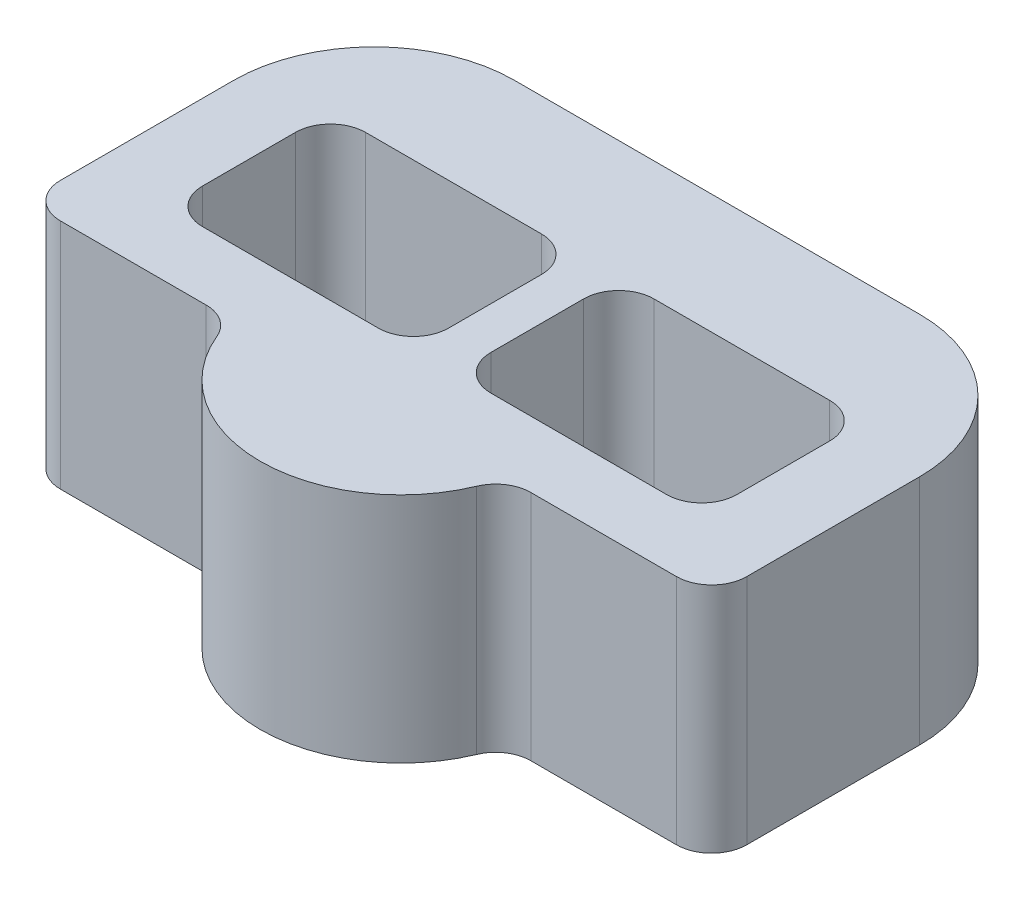
SolidWorks part; units mm, degrees
ref_plane "Front Plane" through (0, 0, 0) normal (0, 0, 1) x (1, 0, 0)
ref_plane "Top Plane" through (0, 0, 0) normal (0, 1, 0) x (1, 0, 0)
ref_plane "Right Plane" through (0, 0, 0) normal (1, 0, 0) x (0, 0, -1)
sketch "Sketch1" plane through (0, 0, 0) normal (0, 1, 0) x (1, 0, 0)
  line L1 (13.208, -13.716) -> (22.733, -13.716) construction
  line L2 (0, -8.255) -> (0, -23.876)
  line L3 (45.6459, -27.051) -> (58.801, -27.051)
  line L4 (61.976, -8.255) -> (61.976, -23.876)
  line L5 (10.033, -6.35) -> (25.908, -6.35) construction
  line L6 (6.858, -9.525) -> (6.858, -17.907) construction
  line L7 (12.7, 4.445) -> (49.276, 4.445)
  line L8 (10.033, -21.082) -> (25.908, -21.082) construction
  line L10 (29.083, -9.525) -> (29.083, -17.907) construction
  line L11 (55.118, -9.525) -> (55.118, -17.907) construction
  line L12 (51.943, -21.082) -> (36.068, -21.082) construction
  line L13 (32.893, -9.525) -> (32.893, -17.907) construction
  line L14 (51.943, -6.35) -> (36.068, -6.35) construction
  line L15 (3.175, -27.051) -> (16.3301, -27.051)
  line L16 (13.208, -10.541) -> (22.733, -10.541)
  line L17 (13.208, -16.891) -> (22.733, -16.891)
  line L18 (30.988, 4.445) -> (30.988, -36.83) construction
  line L19 (48.768, -13.716) -> (39.243, -13.716) construction
  line L20 (48.768, -10.541) -> (39.243, -10.541)
  line L21 (48.768, -16.891) -> (39.243, -16.891)
  arc A0 (19.2617, -29.0068) -> (42.7143, -29.0068) centre (30.988, -24.13) ccw
  arc A3 (0, -8.255) -> (12.7, 4.445) centre (12.7, -8.255) cw
  arc A4 (61.976, -8.255) -> (49.276, 4.445) centre (49.276, -8.255) ccw
  arc A5 (3.175, -27.051) -> (0, -23.876) centre (3.175, -23.876) cw
  arc A6 (58.801, -27.051) -> (61.976, -23.876) centre (58.801, -23.876) ccw
  arc A7 (42.7143, -29.0068) -> (45.6459, -27.051) centre (45.6459, -30.226) cw
  arc A8 (19.2617, -29.0068) -> (16.3301, -27.051) centre (16.3301, -30.226) ccw
  arc A9 (55.118, -17.907) -> (51.943, -21.082) centre (51.943, -17.907) cw construction
  arc A10 (55.118, -9.525) -> (51.943, -6.35) centre (51.943, -9.525) ccw construction
  arc A11 (36.068, -21.082) -> (32.893, -17.907) centre (36.068, -17.907) cw construction
  arc A12 (32.893, -9.525) -> (36.068, -6.35) centre (36.068, -9.525) cw construction
  arc A13 (25.908, -6.35) -> (29.083, -9.525) centre (25.908, -9.525) cw construction
  arc A14 (25.908, -21.082) -> (29.083, -17.907) centre (25.908, -17.907) ccw construction
  arc A15 (6.858, -17.907) -> (10.033, -21.082) centre (10.033, -17.907) ccw construction
  arc A16 (10.033, -6.35) -> (6.858, -9.525) centre (10.033, -9.525) ccw construction
  arc A17 (13.208, -10.541) -> (13.208, -16.891) centre (13.208, -13.716) ccw
  arc A18 (22.733, -16.891) -> (22.733, -10.541) centre (22.733, -13.716) ccw
  arc A19 (48.768, -10.541) -> (48.768, -16.891) centre (48.768, -13.716) cw
  arc A20 (39.243, -16.891) -> (39.243, -10.541) centre (39.243, -13.716) cw
  point P27 (0, 0)
  point P34 (43.3475, -27.051)
  point P55 (17.9705, -13.716)
  point P60 (6.858, -13.716)
  point P65 (44.0055, -13.716)
  dimension "D1" = 12.7
extrude "Boss-Extrude1" add sketch "Sketch1" along normal blind 20.9804
sketch "Sketch2" plane through (0, 20.9804, 0) normal (0, 1, 0) x (1, 0, 0)
  line L0 (6.858, -9.525) -> (6.858, -17.907) construction
  line L1 (10.033, -21.082) -> (25.908, -21.082) construction
  line L2 (29.083, -9.525) -> (29.083, -17.907) construction
  line L3 (10.033, -6.35) -> (25.908, -6.35) construction
  line L4 (6.858, -9.525) -> (6.858, -17.907)
  line L5 (10.033, -21.082) -> (25.908, -21.082)
  line L6 (29.083, -9.525) -> (29.083, -17.907)
  line L7 (10.033, -6.35) -> (25.908, -6.35)
  line L8 (51.943, -6.35) -> (36.068, -6.35) construction
  line L9 (32.893, -9.525) -> (32.893, -17.907) construction
  line L10 (51.943, -21.082) -> (36.068, -21.082) construction
  line L11 (55.118, -9.525) -> (55.118, -17.907) construction
  line L12 (51.943, -6.35) -> (36.068, -6.35)
  line L13 (32.893, -9.525) -> (32.893, -17.907)
  line L14 (51.943, -21.082) -> (36.068, -21.082)
  line L15 (55.118, -9.525) -> (55.118, -17.907)
  arc A0 (10.033, -6.35) -> (6.858, -9.525) centre (10.033, -9.525) ccw construction
  arc A1 (6.858, -17.907) -> (10.033, -21.082) centre (10.033, -17.907) ccw construction
  arc A2 (25.908, -21.082) -> (29.083, -17.907) centre (25.908, -17.907) ccw construction
  arc A3 (29.083, -9.525) -> (25.908, -6.35) centre (25.908, -9.525) ccw construction
  arc A4 (10.033, -6.35) -> (6.858, -9.525) centre (10.033, -9.525) ccw
  arc A5 (6.858, -17.907) -> (10.033, -21.082) centre (10.033, -17.907) ccw
  arc A6 (25.908, -21.082) -> (29.083, -17.907) centre (25.908, -17.907) ccw
  arc A7 (29.083, -9.525) -> (25.908, -6.35) centre (25.908, -9.525) ccw
  arc A8 (55.118, -9.525) -> (51.943, -6.35) centre (51.943, -9.525) ccw construction
  arc A9 (36.068, -6.35) -> (32.893, -9.525) centre (36.068, -9.525) ccw construction
  arc A10 (32.893, -17.907) -> (36.068, -21.082) centre (36.068, -17.907) ccw construction
  arc A11 (51.943, -21.082) -> (55.118, -17.907) centre (51.943, -17.907) ccw construction
  arc A12 (55.118, -9.525) -> (51.943, -6.35) centre (51.943, -9.525) ccw
  arc A13 (36.068, -6.35) -> (32.893, -9.525) centre (36.068, -9.525) ccw
  arc A14 (32.893, -17.907) -> (36.068, -21.082) centre (36.068, -17.907) ccw
  arc A15 (51.943, -21.082) -> (55.118, -17.907) centre (51.943, -17.907) ccw
extrude "Cut-Extrude1" cut sketch "Sketch2" against normal offset from surface (15.9004 mm away) 5.08 up to face at (30.988, 0, 18.7149)
sketch "Sketch3" plane through (0, 20.9804, 0) normal (0, 1, 0) x (1, 0, 0)
  line L0 (30.988, -36.83) -> (30.988, -54.2925) construction
  line L1 (-6.35, 21.9075) -> (68.326, 21.9075)
  line L2 (-6.35, 21.9075) -> (-6.35, -54.2925)
  line L3 (-6.35, -54.2925) -> (68.326, -54.2925)
  line L4 (68.326, 21.9075) -> (68.326, -54.2925)
  line L5 (30.988, 4.445) -> (30.988, 21.9075) construction
  line L6 (0, -8.255) -> (0, -23.876) construction
  line L7 (61.976, -8.255) -> (61.976, -23.876) construction
  point P18 (30.988, 4.445)
  point P19 (30.988, -36.83)
  dimension "D1" = 76.2
  dimension "D2" = 6.35
  dimension "D3" = 6.35
sketch "Sketch4" plane through (0, 0, 0) normal (0, -1, 0) x (1, 0, 0)
  line L0 (-6.35, -21.9075) -> (68.326, -21.9075) construction
  line L1 (68.326, -21.9075) -> (68.326, 54.2925) construction
  line L2 (-6.35, 54.2925) -> (68.326, 54.2925) construction
  line L3 (-6.35, -21.9075) -> (-6.35, 54.2925) construction
  line L4 (-6.35, -21.9075) -> (68.326, -21.9075)
  line L5 (68.326, -21.9075) -> (68.326, 54.2925)
  line L6 (-6.35, 54.2925) -> (68.326, 54.2925)
  line L7 (-6.35, -21.9075) -> (-6.35, 54.2925)
